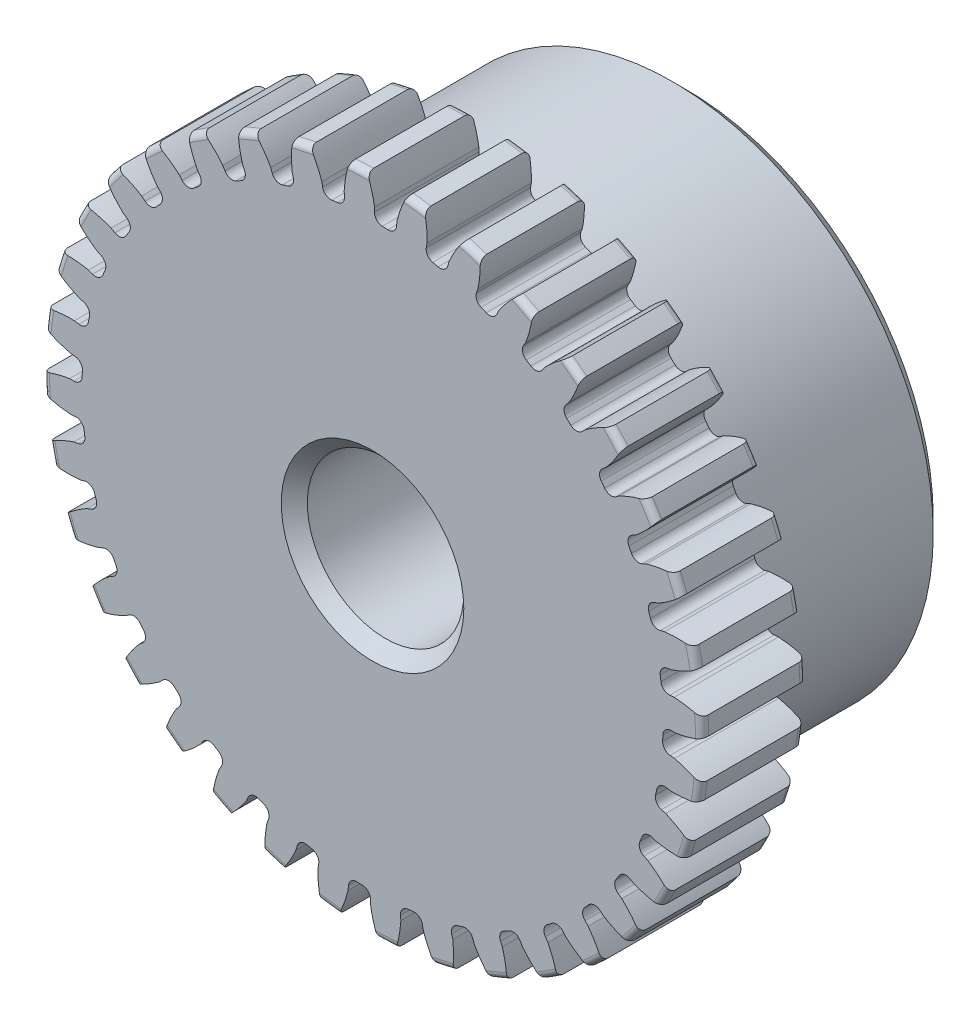
SolidWorks part; units mm, degrees
ref_plane "Front" through (0, 0, 0) normal (0, 0, 1) x (1, 0, 0)
ref_plane "Top" through (0, 0, 0) normal (0, 1, 0) x (1, 0, 0)
ref_plane "Right" through (0, 0, 0) normal (1, 0, 0) x (0, 0, -1)
sketch "Sketch1" plane through (0, 0, 0) normal (0, 0, 1) x (1, 0, 0)
  line L0 (-457.2, 0) -> (457.2, 0) construction
  circle A0 centre (0, 0) radius 10.033
  circle A1 centre (0, 0) radius 9.525 construction
  circle A3 centre (0, 0) radius 8.8424 construction
  dimension "D1" = 1.1906
  dimension "OD" = 20.066
  dimension "Ptich Dia" = 19.05
  dimension "Root Dia" = 17.6847
  dimension "D3" = 0.508
  dimension "Number of Teeth" = 914.4
extrude "Boss-Extrude1" add sketch "Sketch1" against normal blind 3.175
sketch "Sketch2" plane through (0, 0, 0) normal (1, 0, 0) x (0, 0, -1)
  line L0 (3.175, 0) -> (9.525, 0)
  line L1 (3.175, 0) -> (3.175, 7.9375)
  line L2 (3.175, 7.9375) -> (9.525, 7.9375)
  line L3 (9.525, 7.9375) -> (9.525, 0)
  point P5 (9.525, -7.9375)
  point P6 (0, -10.033)
  point P7 (3.175, -10.033)
  point P9 (0, 10.033)
  dimension "Face Wd" = 3.175
  dimension "B Hub Dia" = 15.875
  dimension "D O'all Lg." = 9.525
revolve "Revolve1" add sketch "Sketch2" angle 360 about L0
fillet "Fillet2" radius 0.2007 3 edges at (10.033, 0, -3.175) (10.033, 0, 0) (7.9375, 0, -3.175)
sketch "Sketch3" plane through (0, 0, 0) normal (0, 0, 1) x (1, 0, 0)
  line L0 (0, 0) -> (0, 10.033) construction
  line L1 (-2.3089, 8.9279) -> (0, 9.525)
  line L2 (-9.5921, 9.525) -> (9.5921, 9.525) construction
  line L3 (-9.2865, 7.1233) -> (9.2865, 11.9267) construction
  line L4 (-2.3089, 8.9279) -> (0, 0) construction
  line L5 (-5.8892, 7.0961) -> (0, 0) construction
  line L6 (-5.8892, 7.0961) -> (-0.9538, 11.1922) construction
  line L7 (-1.61, 9.08) -> (0, 0) construction
  line L8 (-1.61, 9.08) -> (0.0338, 9.3714) construction
  arc A0 (-2.3089, 8.9279) -> (-5.8892, 7.0961) centre (0, 0) ccw
  circle A1 centre (0, 0) radius 9.525 construction
  circle A2 centre (0, 0) radius 9.2216 construction
  arc A3 (-2.3089, 8.9279) -> (-1.61, 9.08) centre (0, 0) cw
  circle A4 centre (0, 0) radius 10.033 construction
  point P6 (0, 9.525)
  dimension "D1" = 2.3849
  dimension "Pressure Angle" = 14.5
  dimension "D2" = 4.0543
  dimension "D3" = 6.4137
  dimension "D4" = 0.7155
  dimension "D5" = 1.6694
sketch "Sketch4" plane through (0, 0, 0) normal (0, 0, 1) x (1, 0, 0)
  line L0 (0, 0) -> (0.4151, 9.5069) construction
  line L1 (0.0598, 9.2214) -> (0.0598, 8.8422)
  line L2 (0, 9.525) -> (0.8302, 9.4888) construction
  line L3 (0.7441, 9.1915) -> (0.7111, 8.8137)
  line L4 (0.0598, 8.8422) -> (0, 0) construction
  line L5 (0, 0) -> (0, 10.033) construction
  line L6 (-5.8892, 7.0961) -> (-0.9538, 11.1922) construction
  line L7 (-5.8892, 7.0961) -> (-0.9538, 11.1922) construction
  arc A0 (0.7111, 8.8137) -> (0.0598, 8.8422) centre (0, 0) ccw
  arc A1 (0, 9.525) -> (0.8302, 9.4888) centre (0, 0) cw construction
  circle A2 centre (0, 0) radius 9.525 construction
  circle A3 centre (0, 0) radius 9.2216 construction
  circle A4 centre (0, 0) radius 8.8424 construction
  arc A5 (1.9256, 11.0664) -> (-0.9538, 11.1922) centre (0, 0) ccw
  spline S0 degree 2 poles (-0.9538, 11.1922) (-0.1068, 10.325) (0.0598, 9.2214) knots 0 0 0 1 1 1
  spline S1 degree 2 poles (1.9256, 11.0664) (1.0063, 10.2764) (0.7441, 9.1915) knots 0 0 0 1 1 1
  dimension "D1" = 0.8312
extrude "Cut-Extrude1" cut sketch "Sketch4" against normal through all
fillet "Fillet1" radius 0.2494 2 edges at (0.7111, 8.8137, -1.5875) (0.0598, 8.8422, -1.5875)
pattern_circular "CirPattern1" count 36 over 360 about axis through (0, 0, -3.175) along (0, 0, 1) of "Cut-Extrude1", "Fillet1"
sketch "Sketch5" plane through (0, 0, 0) normal (0, 0, 1) x (1, 0, 0)
  circle A0 centre (0, 0) radius 2.3813
  circle A1 centre (0, 0) radius 1.5875 construction
  dimension "Bore Min" = 4.7625
  dimension "Bore Max" = 3.175
extrude "Cut-Extrude2" cut sketch "Sketch5" against normal through all
chamfer "Chamfer1" distance 0.3969 angle 45 3 edges at (7.9375, 0, -9.525) (2.3813, 0, 0) (2.3813, 0, -9.525)
sketch "Pitch Dia" plane through (0, 0, 0) normal (0, 0, 1) x (1, 0, 0)
  circle A0 centre (0, 0) radius 9.525 construction
  circle A1 centre (0, 0) radius 9.525 construction
equation "\"D1@Boss-Extrude1\" = \"Face Wd@Sketch2\""
equation "\"D2@Sketch3\" = \"D1@Sketch3\"*1.7"
equation "\"D3@Sketch3\" = \"D1@Sketch3\"+\"D2@Sketch3\"-.001"
equation "\"D4@Sketch3\" = \"D1@Sketch3\"*.3"
equation "\"D5@Sketch3\" = \"D1@Sketch3\"-\"D4@Sketch3\""
equation "\"D1@Sketch4\" = 1.5708/(\"Number of Teeth@Sketch1\"/\"Ptich Dia@Sketch1\")"
equation "\"D1@Chamfer1\" = \"B Hub Dia@Sketch2\"*.025"
equation "\"D1@CirPattern1\" = \"Number of Teeth@Sketch1\""
equation "\"D1@Fillet1\" = \"D1@Sketch4\"*.3"
equation "\"D1@Fillet2\" = \"OD@Sketch1\"*.01"
equation "\"D1@Sketch1\" = 2.250/(\"Number of Teeth@Sketch1\"/\"Ptich Dia@Sketch1\")"
